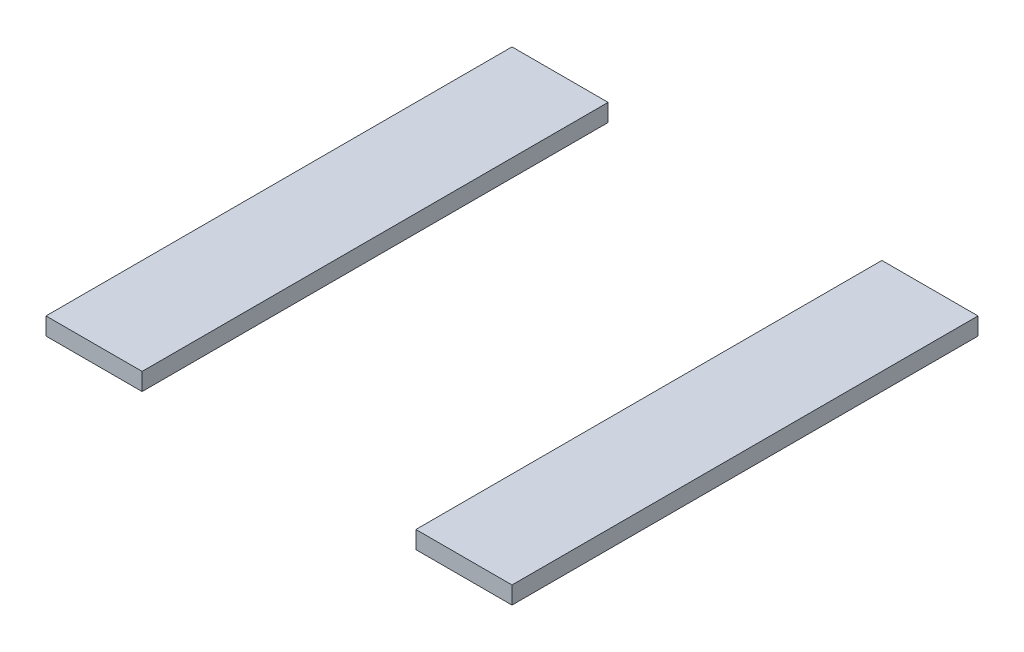
SolidWorks part; units mm, degrees
ref_plane "Front Plane" through (0, 0, 0) normal (0, 0, 1) x (1, 0, 0)
ref_plane "Top Plane" through (0, 0, 0) normal (0, 1, 0) x (1, 0, 0)
ref_plane "Right Plane" through (0, 0, 0) normal (1, 0, 0) x (0, 0, -1)
sketch "Sketch1" plane through (0, 0, 0) normal (0, 1, 0) x (1, 0, 0)
  line L0 (16.5, 0) -> (16.5, 80)
  line L1 (0, 0) -> (80, 0) construction
  line L2 (0, 0) -> (0, 80)
  line L3 (0, 80) -> (80, 80) construction
  line L4 (80, 0) -> (80, 80)
  line L6 (63.5, 80) -> (63.5, 0)
  line L7 (63.5, 0) -> (63.5, 80) construction
  line L8 (16.5, 0) -> (16.5, 80) construction
  line L9 (40, 80) -> (40, 0) construction
  line L10 (16.5, 0) -> (0, 0)
  line L11 (63.5, 0) -> (80, 0)
  line L12 (80, 80) -> (63.5, 80)
  line L13 (16.5, 80) -> (0, 80)
sketch "Sketch2" plane through (0, 0, 0) normal (1, 0, 0) x (0, 0, -1)
  line L1 (80, 3) -> (0, 3)
  line L2 (80, 3) -> (80, 0)
  line L3 (80, 0) -> (0, 0)
  line L4 (0, 3) -> (0, 0)
extrude "Boss-Extrude1" add sketch "Sketch1" along normal up to vertex (3 mm away) up to point (0, 3, 0)
